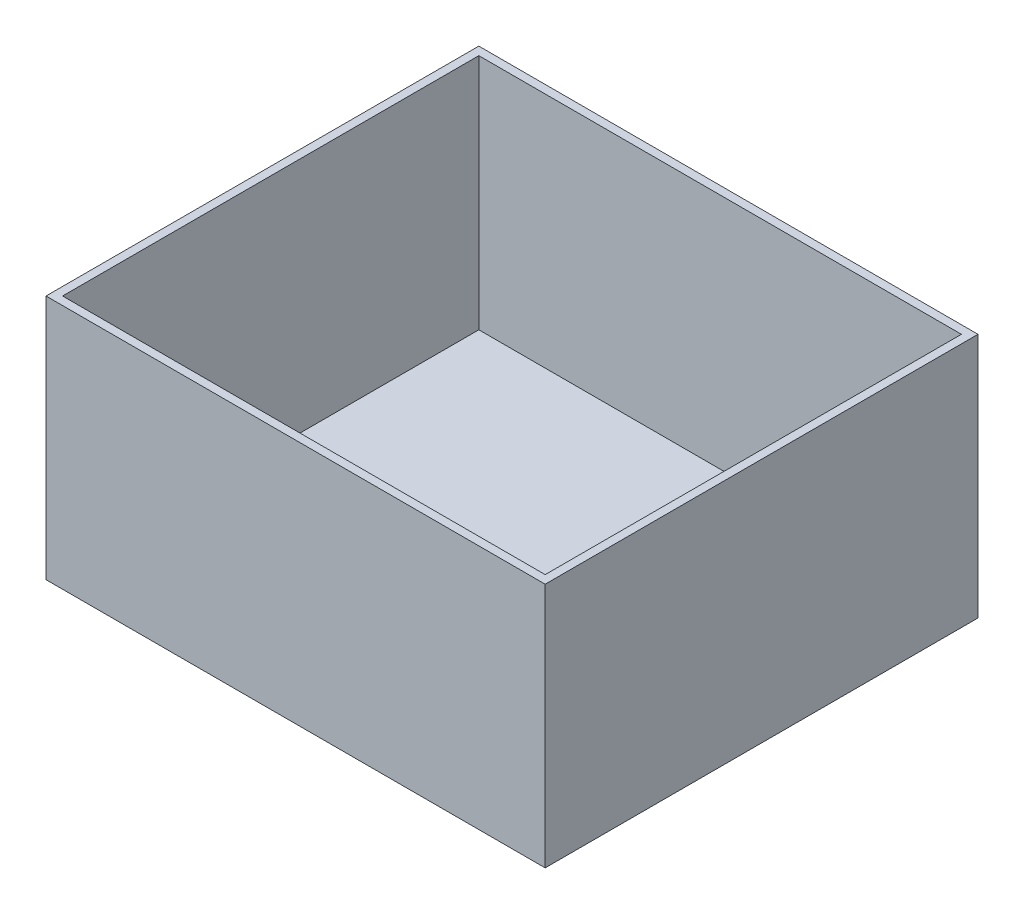
SolidWorks part; units mm, degrees
ref_plane "Front Plane" through (0, 0, 0) normal (0, 0, 1) x (1, 0, 0)
ref_plane "Top Plane" through (0, 0, 0) normal (0, 1, 0) x (1, 0, 0)
ref_plane "Right Plane" through (0, 0, 0) normal (1, 0, 0) x (0, 0, -1)
sketch "Sketch1" plane through (0, 1.9566, 0) normal (0, 1, 0) x (1, 0, 0)
  line L4 (157.1774, 47.6955) -> (6.6774, 47.6955)
  line L5 (6.6774, 47.6955) -> (6.6774, -82.8045)
  line L6 (6.6774, -82.8045) -> (157.1774, -82.8045)
  line L7 (157.1774, -82.8045) -> (157.1774, 47.6955)
  line L8 (9.1774, -80.3045) -> (154.6774, -80.3045)
  line L9 (154.6774, -80.3045) -> (154.6774, 45.1955)
  line L10 (154.6774, 45.1955) -> (9.1774, 45.1955)
  line L11 (9.1774, 45.1955) -> (9.1774, -80.3045)
  line L12 (9.1774, -80.3045) -> (154.6774, -80.3045)
  line L13 (154.6774, -80.3045) -> (154.6774, 45.1955)
  line L14 (154.6774, 45.1955) -> (9.1774, 45.1955)
  line L15 (9.1774, 45.1955) -> (9.1774, -80.3045)
  dimension "D1" = 0.25
  dimension "D2" = 2.5
extrude "Boss-Extrude1" add sketch "Sketch1" against normal offset from surface (71.58 mm away) 2
sketch "Sketch3" plane through (0, -69.6234, 0) normal (0, -1, 0) x (-1, 0, 0)
  line L1 (-6.6774, 47.6955) -> (-157.1774, 47.6955)
  line L2 (-6.6774, 47.6955) -> (-6.6774, -82.8045)
  line L3 (-6.6774, -82.8045) -> (-157.1774, -82.8045)
  line L4 (-157.1774, 47.6955) -> (-157.1774, -82.8045)
extrude "Boss-Extrude2" add sketch "Sketch3" along normal blind 2.5
